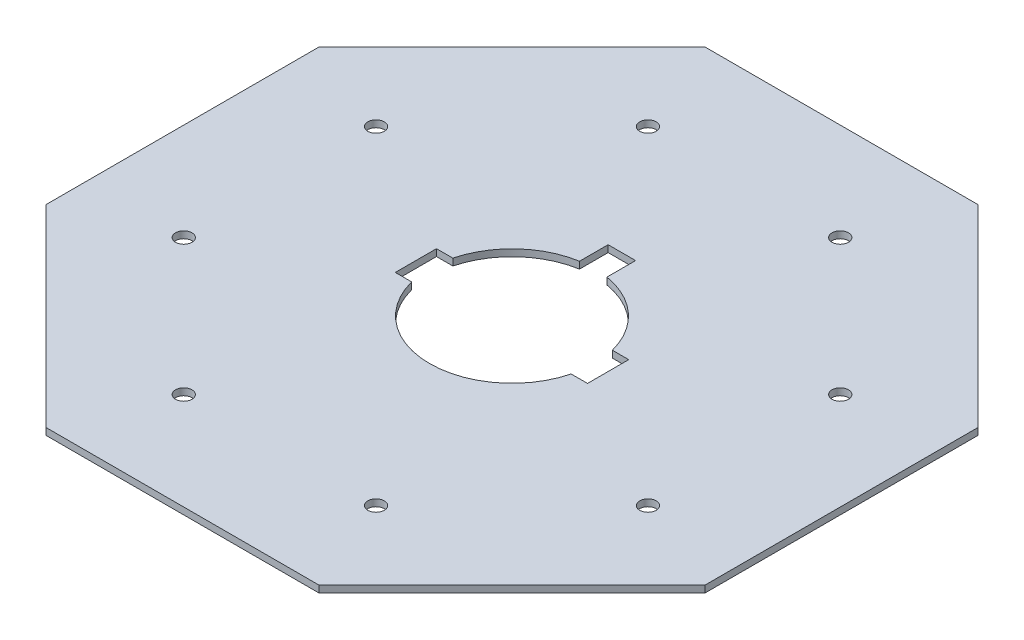
SolidWorks part; units mm, degrees
ref_plane "Front Plane" through (0, 0, 0) normal (0, 0, 1) x (1, 0, 0)
ref_plane "Top Plane" through (0, 0, 0) normal (0, 1, 0) x (1, 0, 0)
ref_plane "Right Plane" through (0, 0, 0) normal (1, 0, 0) x (0, 0, -1)
sketch "Sketch1" plane through (0, 0, 0) normal (0, 1, 0) x (1, 0, 0)
  line L0 (-2.3657, 0) -> (-2.3657, 182.3554) construction
  line L1 (63.1261, 152.4) -> (-63.1261, 152.4)
  line L2 (-63.1261, 152.4) -> (-152.4, 63.1261)
  line L3 (-152.4, 63.1261) -> (-152.4, -63.1261)
  line L4 (-152.4, -63.1261) -> (-63.1261, -152.4)
  line L5 (-63.1261, -152.4) -> (63.1261, -152.4)
  line L6 (63.1261, -152.4) -> (152.4, -63.1261)
  line L7 (152.4, -63.1261) -> (152.4, 63.1261)
  line L8 (152.4, 63.1261) -> (63.1261, 152.4)
  circle A0 centre (0, 0) radius 152.4 construction
  dimension "D1" = 304.8
extrude "Boss-Extrude1" add sketch "Sketch1" along normal blind 3.175
sketch "Sketch2" plane through (0, 3.175, 0) normal (0, 1, 0) x (1, 0, 0)
  circle A0 centre (0, 0) radius 38.1
  dimension "D1" = 76.2
extrude "Cut-Extrude1" cut sketch "Sketch2" against normal through all both and the other way through all
sketch "Sketch3" plane through (0, 3.175, 0) normal (0, 1, 0) x (1, 0, 0)
  line L0 (0, 0) -> (63.1261, -152.4) construction
  circle A0 centre (44.4634, -107.3442) radius 3.81
  circle A1 centre (-44.4634, -107.3442) radius 3.81
  circle A2 centre (-107.3442, -44.4634) radius 3.81
  circle A3 centre (-107.3442, 44.4634) radius 3.81
  circle A4 centre (-44.4634, 107.3442) radius 3.81
  circle A5 centre (44.4634, 107.3442) radius 3.81
  circle A6 centre (107.3442, 44.4634) radius 3.81
  circle A7 centre (107.3442, -44.4634) radius 3.81
  point P23 (0, 0)
  dimension "D1" = 7.62
  dimension "D2" = 48.768
  dimension "D3" = 8
extrude "Cut-Extrude2" cut sketch "Sketch3" against normal through all
sketch "Sketch4" plane through (0, 3.175, 0) normal (0, 1, 0) x (1, 0, 0)
  line L1 (-44.45, -9.525) -> (-31.75, -9.525)
  line L2 (-44.45, -9.525) -> (-44.45, 9.525)
  line L3 (-44.45, 9.525) -> (-31.75, 9.525)
  line L4 (-31.75, -9.525) -> (-31.75, 9.525)
  line L5 (-44.45, -9.525) -> (-31.75, 9.525) construction
  line L6 (-44.45, 9.525) -> (-31.75, -9.525) construction
  line L7 (31.75, -9.525) -> (44.45, -9.525)
  line L8 (31.75, -9.525) -> (31.75, 9.525)
  line L9 (31.75, 9.525) -> (44.45, 9.525)
  line L10 (44.45, -9.525) -> (44.45, 9.525)
  line L11 (31.75, -9.525) -> (44.45, 9.525) construction
  line L12 (31.75, 9.525) -> (44.45, -9.525) construction
  line L13 (-6.35, 25.4) -> (6.35, 25.4)
  line L14 (-6.35, 25.4) -> (-6.35, 50.8)
  line L15 (-6.35, 50.8) -> (6.35, 50.8)
  line L16 (6.35, 25.4) -> (6.35, 50.8)
  line L17 (-6.35, 25.4) -> (6.35, 50.8) construction
  line L18 (-6.35, 50.8) -> (6.35, 25.4) construction
  circle A0 centre (0, 0) radius 38.1 construction
  point P0 (-38.1, 0)
  point P7 (38.1, 0)
  point P12 (0, 38.1)
  dimension "D1" = 12.7
  dimension "D2" = 19.05
  dimension "D3" = 19.05
  dimension "D4" = 12.7
  dimension "D5" = 6.35
  dimension "D6" = 6.35
extrude "Cut-Extrude3" cut sketch "Sketch4" against normal through all
